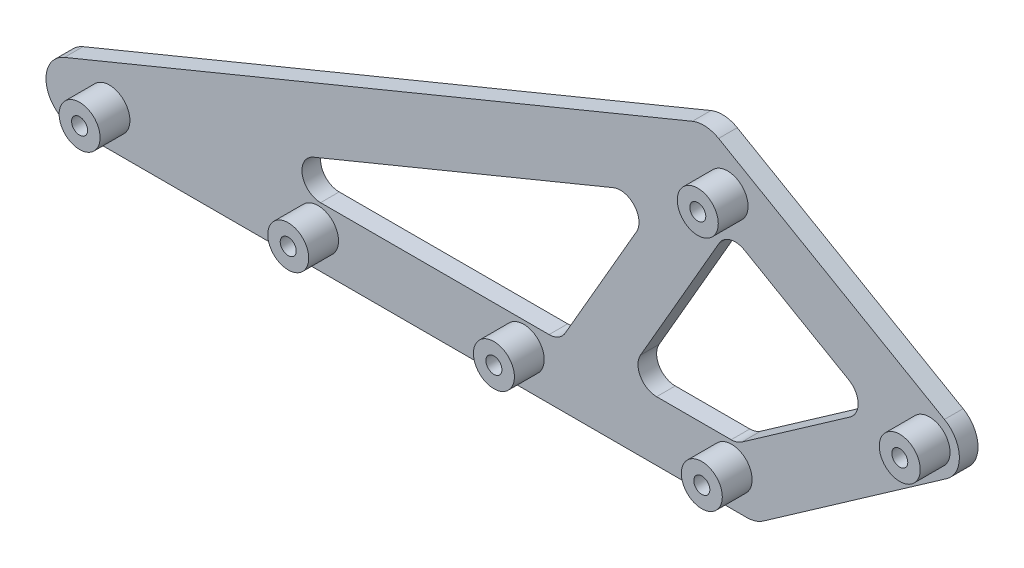
SolidWorks part; units mm, degrees
material "ABS"
ref_plane "Front" through (0, 0, 0) normal (0, 0, 1) x (1, 0, 0)
ref_plane "Top" through (0, 0, 0) normal (0, 1, 0) x (1, 0, 0)
ref_plane "Right" through (0, 0, 0) normal (1, 0, 0) x (0, 0, -1)
sketch "Sketch1" plane through (0, 0, 0) normal (0, 0, 1) x (1, 0, 0)
  line L0 (0, 0) -> (180, 0) construction
  line L1 (0, 8) -> (180, 8)
  line L2 (0, -8) -> (180, -8)
  line L3 (180, 0) -> (229.1491, 34.4146) construction
  line L6 (175.4114, 6.5532) -> (224.5605, 40.9678)
  line L9 (184.5886, -6.5532) -> (233.7377, 27.8614)
  line L12 (229.1491, 34.4146) -> (168.5273, 69.4146) construction
  line L13 (225.1491, 27.4864) -> (164.5273, 62.4864)
  line L14 (233.1491, 41.3428) -> (172.5273, 76.3428)
  line L15 (0, 0) -> (168.5273, 69.4146) construction
  line L16 (-3.0468, 7.3971) -> (165.4806, 76.8117)
  line L17 (3.0468, -7.3971) -> (171.5741, 62.0175)
  arc A0 (0, 8) -> (0, -8) centre (0, 0) ccw
  arc A1 (180, -8) -> (180, 8) centre (180, 0) ccw
  arc A8 (175.4114, 6.5532) -> (184.5886, -6.5532) centre (180, 0) ccw
  arc A9 (233.7377, 27.8614) -> (224.5605, 40.9678) centre (229.1491, 34.4146) ccw
  arc A10 (225.1491, 27.4864) -> (233.1491, 41.3428) centre (229.1491, 34.4146) ccw
  arc A11 (172.5273, 76.3428) -> (164.5273, 62.4864) centre (168.5273, 69.4146) ccw
  arc A12 (-3.0468, 7.3971) -> (3.0468, -7.3971) centre (0, 0) ccw
  arc A13 (171.5741, 62.0175) -> (165.4806, 76.8117) centre (168.5273, 69.4146) ccw
  point P3 (90, 0)
  point P10 (204.5746, 17.2073)
  point P17 (198.8382, 51.9146)
  point P22 (84.2637, 34.7073)
  dimension "D2" = 8
  dimension "D1" = 180
  dimension "D3" = 60
  dimension "D4" = 35
  dimension "D5" = 70
  dimension "D6" = 30
extrude "Boss-Extrude1" add sketch "Sketch1" along normal blind 5 contours A12 L13 A9 L9 L14 L17 | A11 L14 L17 L1 A1 L16 | A13 L17 L1 L9 A8 L2 | A10 L6 A0 L1 L9 L14 | L17 A13 A1 L1 | A11 A12 L17 L14 | A9 A10 L14 L9 | A0 A8 L9 L1
sketch "Sketch2" plane through (0, 0, 5) normal (0, 0, 1) x (1, 0, 0)
  line L0 (214.274, 33.7651) -> (167.9354, 60.5187) construction
  line L1 (177.4776, 8) -> (214.274, 33.7651) construction
  line L2 (40.4284, 8) -> (177.4776, 8) construction
  line L3 (214.274, 33.7651) -> (167.9354, 60.5187)
  line L4 (177.4776, 8) -> (214.274, 33.7651)
  line L5 (40.4284, 8) -> (177.4776, 8)
  line L6 (40.4284, 8) -> (167.9354, 60.5187) construction
  line L7 (40.4284, 8) -> (167.9354, 60.5187)
  line L8 (157.8266, 56.355) -> (129.9088, 8)
  line L9 (175.1471, 56.355) -> (147.2293, 8)
  line M15 (167.9354, 60.5187) -> (214.274, 33.7651)
  dimension "D1" = 60
  dimension "D2" = 15
extrude "Boss-Extrude2" add sketch "Sketch2" against normal up to surface (5 mm away) contours L9 L7 L8 L5 M15 up to face at (145.497, 25.8224, 0)
fillet "Fillet1" radius 5 7 edges at (214.274, 33.7651, 2.5) (175.1471, 56.355, 2.5) (147.2293, 8, 2.5) (40.4284, 8, 2.5) (177.4776, 8, 2.5) (129.9088, 8, 2.5) (157.8266, 56.355, 2.5)
sketch "Sketch3" plane through (0, 0, 5) normal (0, 0, 1) x (1, 0, 0)
  line L0 (176.0183, 1.5) -> (229.1491, 34.4146) construction
  line L1 (0, -8) -> (180, -8) construction
  line L2 (120.2183, 1.5) -> (176.0183, 1.5) construction
  line L3 (65.0183, 1.5) -> (120.2183, 1.5) construction
  line L4 (9.0183, 1.5) -> (65.0183, 1.5) construction
  arc A0 (233.7377, 27.8614) -> (233.1491, 41.3428) centre (229.1491, 34.4146) ccw construction
  arc A1 (233.7377, 27.8614) -> (233.1491, 41.3428) centre (229.1491, 34.4146) ccw
  circle A2 centre (229.1491, 34.4146) radius 2.15
  circle A3 centre (229.1491, 34.4146) radius 5.5
  circle A4 centre (176.0183, 1.5) radius 2.15
  circle A5 centre (176.0183, 1.5) radius 5.5
  circle A6 centre (120.2183, 1.5) radius 2.15
  circle A7 centre (120.2183, 1.5) radius 5.5
  circle A8 centre (65.0183, 1.5) radius 2.15
  circle A9 centre (65.0183, 1.5) radius 5.5
  circle A10 centre (9.0183, 1.5) radius 2.15
  circle A11 centre (9.0183, 1.5) radius 5.5
  circle A12 centre (174.9378, 64.5) radius 2.15
  circle A13 centre (174.9378, 64.5) radius 5.5
  dimension "D1" = 4.3
  dimension "D2" = 11
  dimension "D3" = 62.5
  dimension "D4" = 9.5
  dimension "D5" = 55.8
  dimension "D6" = 111
  dimension "D7" = 167
  dimension "D8" = 62
  dimension "D9" = 72.5
extrude "Boss-Extrude3" add sketch "Sketch3" along normal blind 8 contours A13 A12 | A3 A2 | A5 A4 | A7 A6 | A9 A8 | A11 A10
sketch "Sketch4" plane through (0, 0, 5) normal (0, 0, 1) x (1, 0, 0)
  circle A0 centre (9.0183, 1.5) radius 2.15 construction
  circle A1 centre (9.0183, 1.5) radius 2.15
  circle A2 centre (65.0183, 1.5) radius 2.15 construction
  circle A3 centre (65.0183, 1.5) radius 2.15
  circle A4 centre (176.0183, 1.5) radius 2.15 construction
  circle A5 centre (120.2183, 1.5) radius 2.15
  circle A6 centre (120.2183, 1.5) radius 2.15
  circle A7 centre (176.0183, 1.5) radius 2.15
  circle A8 centre (229.1491, 34.4146) radius 2.15 construction
  circle A9 centre (229.1491, 34.4146) radius 2.15
  circle A10 centre (174.9378, 64.5) radius 2.15 construction
  circle A11 centre (174.9378, 64.5) radius 2.15
  dimension "D1" = 0
extrude "Cut-Extrude1" cut sketch "Sketch4" against normal through all
sketch "Sketch5" plane through (0, 0, 0) normal (0, 0, -1) x (-1, 0, 0)
  circle A0 centre (-9.0183, 1.5) radius 2.15 construction
  circle A1 centre (-65.0183, 1.5) radius 2.15 construction
  circle A2 centre (-120.2183, 1.5) radius 2.15 construction
  circle A3 centre (-176.0183, 1.5) radius 2.15 construction
  circle A4 centre (-174.9378, 64.5) radius 2.15 construction
  circle A5 centre (-229.1491, 34.4146) radius 2.15 construction
  circle A6 centre (-9.0183, 1.5) radius 2.15
  circle A7 centre (-65.0183, 1.5) radius 2.15
  circle A8 centre (-120.2183, 1.5) radius 2.15
  circle A9 centre (-176.0183, 1.5) radius 2.15
  circle A10 centre (-174.9378, 64.5) radius 2.15
  circle A11 centre (-229.1491, 34.4146) radius 2.15
  circle A12 centre (-174.9378, 64.5) radius 4
  circle A13 centre (-229.1491, 34.4146) radius 4
  circle A14 centre (-176.0183, 1.5) radius 4
  circle A15 centre (-120.2183, 1.5) radius 4
  circle A16 centre (-65.0183, 1.5) radius 4
  circle A17 centre (-9.0183, 1.5) radius 4
  dimension "D1" = 8
extrude "Cut-Extrude2" [suppressed] cut sketch "Sketch5" against normal blind 2
fillet "Fillet2" [suppressed] radius 1
